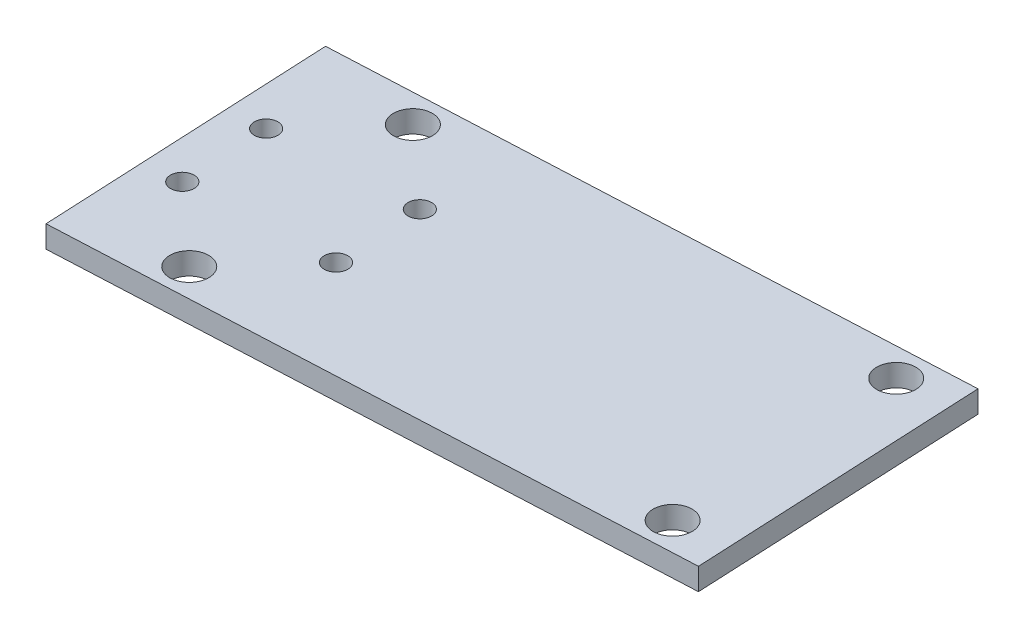
SolidWorks part; units mm, degrees
ref_plane "前视基准面" through (0, 0, 0) normal (0, 0, 1) x (1, 0, 0)
ref_plane "上视基准面" through (0, 0, 0) normal (0, 1, 0) x (1, 0, 0)
ref_plane "右视基准面" through (0, 0, 0) normal (1, 0, 0) x (0, 0, -1)
sketch "草图1" plane through (0, 0, 0) normal (0, 1, 0) x (1, 0, 0)
  line L0 (-0.2395, 20.5431) -> (1.6592, -19.4118) construction
  line L1 (-15.2226, 19.8311) -> (14.7436, 21.2551)
  line L2 (-15.2226, 19.8311) -> (-13.3239, -20.1238)
  line L3 (-13.3239, -20.1238) -> (16.6423, -18.6998)
  line L4 (14.7436, 21.2551) -> (16.6423, -18.6998) construction
  line L5 (14.7436, 21.2551) -> (69.5757, 23.8608)
  line L6 (69.5757, 23.8608) -> (71.4744, -16.0941)
  line L7 (71.4744, -16.0941) -> (16.6423, -18.6998)
  line L8 (70.7793, -1.4679) -> (70.9218, -4.4646) construction
  line L9 (62.7735, 19.533) -> (64.2924, -12.4309) construction
  line L10 (-14.2732, -0.1463) -> (70.5251, 3.8833) construction
  circle A0 centre (-0.0496, 16.5476) radius 2.65
  circle A1 centre (1.4693, -15.4163) radius 2.65
  circle A2 centre (-8.9941, -5.9022) radius 1.6
  circle A3 centre (-9.5637, 6.0842) radius 1.6
  circle A4 centre (10.4138, 7.0336) radius 1.6
  circle A5 centre (10.9834, -4.9529) radius 1.6
  circle A6 centre (62.7735, 19.533) radius 2.65
  circle A7 centre (64.2924, -12.4309) radius 2.65
  dimension "D3" = 32
  dimension "D4" = 4
  dimension "D5" = 5
  dimension "D7" = 5
  dimension "D8" = 14
  dimension "D9" = 3.2
  dimension "D10" = 5.3
  dimension "D12" = 5.3
  dimension "D14" = 16
  dimension "D1" = 40
  dimension "D2" = 30
  dimension "D6" = 14
  dimension "D11" = 7
  dimension "D13" = 16
extrude "凸台-拉伸1" add sketch "草图1" along normal blind 3
